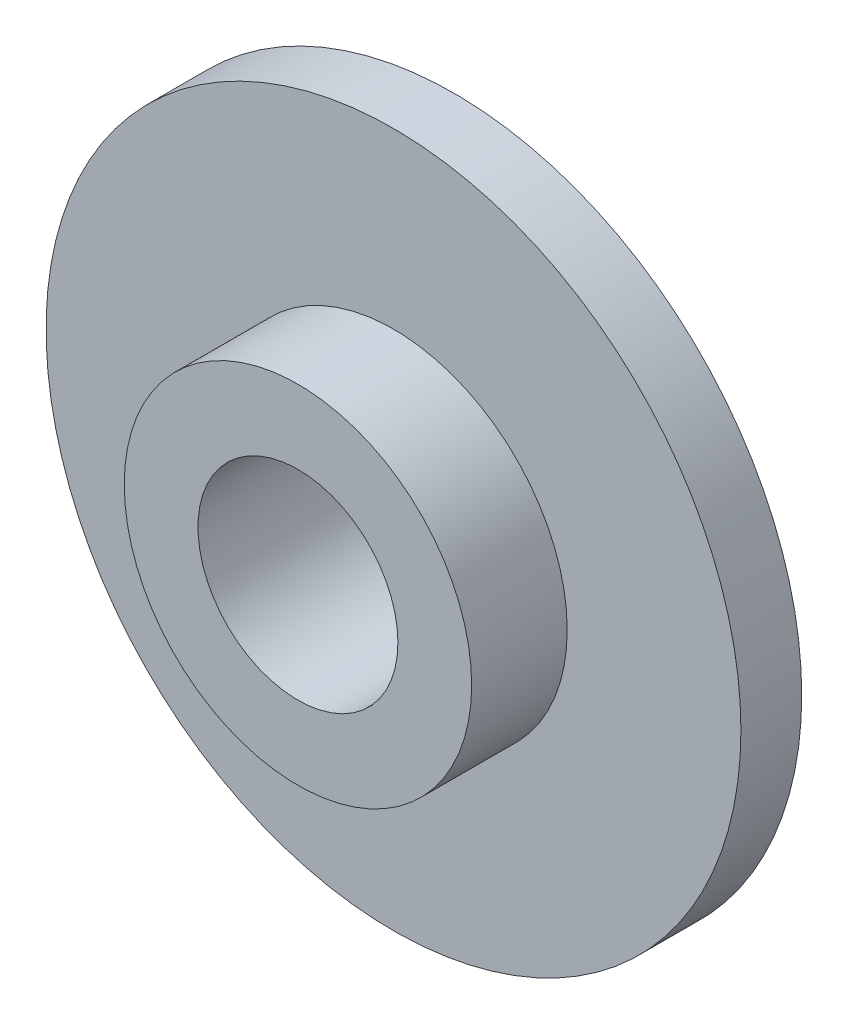
SolidWorks part; units mm, degrees
ref_plane "Front Plane" through (0, 0, 0) normal (0, 0, 1) x (1, 0, 0)
ref_plane "Top Plane" through (0, 0, 0) normal (0, 1, 0) x (1, 0, 0)
ref_plane "Right Plane" through (0, 0, 0) normal (1, 0, 0) x (0, 0, -1)
sketch "Sketch1" plane through (0, 0, 0) normal (0, 0, 1) x (1, 0, 0)
  circle A0 centre (0, 0) radius 10.16
extrude "Boss-Extrude1" add sketch "Sketch1" along normal blind 1.778
sketch "Sketch2" plane through (0, 0, 1.778) normal (0, 0, 1) x (1, 0, 0)
  circle A0 centre (0, 0) radius 5.08
extrude "Boss-Extrude2" add sketch "Sketch2" along normal blind 2.794
sketch "Sketch3" plane through (0, 0, 4.572) normal (0, 0, 1) x (1, 0, 0)
  circle A0 centre (0, 0) radius 2.9235
extrude "Cut-Extrude1" cut sketch "Sketch3" against normal blind 4.572
